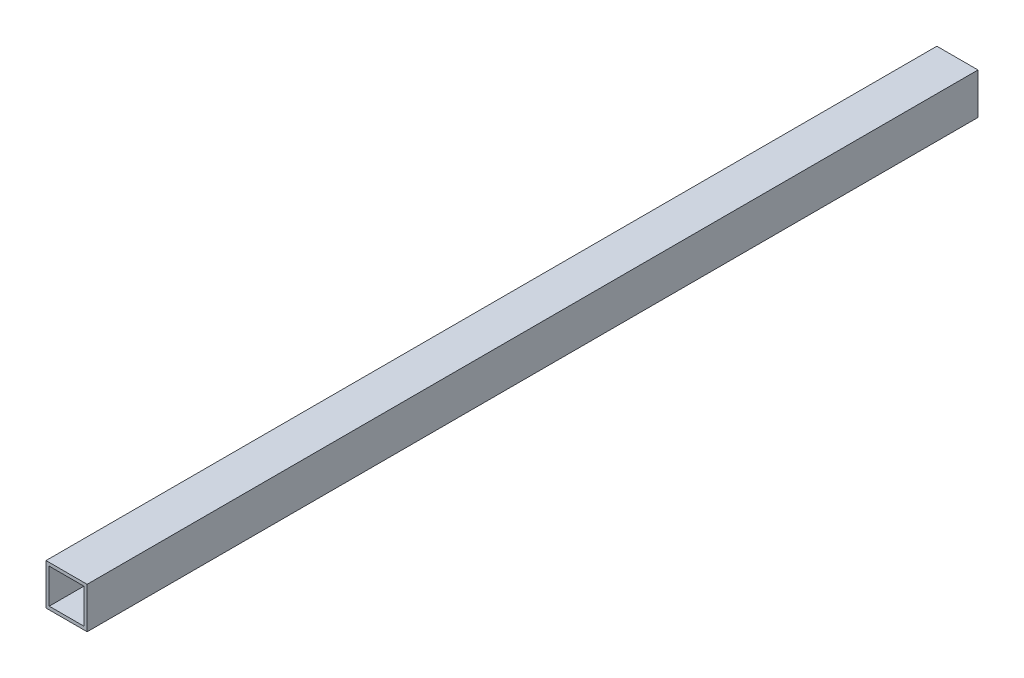
SolidWorks part; units mm, degrees
ref_plane "Front Plane" through (0, 0, 0) normal (0, 0, 1) x (1, 0, 0)
ref_plane "Top Plane" through (0, 0, 0) normal (0, 1, 0) x (1, 0, 0)
ref_plane "Right Plane" through (0, 0, 0) normal (1, 0, 0) x (0, 0, -1)
sketch "Sketch1" plane through (0, 0, 0) normal (0, 0, 1) x (1, 0, 0)
  line L0 (-10.7, 10.7) -> (10.7, 10.7)
  line L1 (-12.7, -12.7) -> (12.7, -12.7)
  line L2 (-12.7, -12.7) -> (-12.7, 12.7)
  line L3 (-12.7, 12.7) -> (12.7, 12.7)
  line L4 (12.7, -12.7) -> (12.7, 12.7)
  line L5 (-12.7, -12.7) -> (12.7, 12.7) construction
  line L6 (-12.7, 12.7) -> (12.7, -12.7) construction
  line L7 (10.7, -10.7) -> (10.7, 10.7)
  line L8 (-10.7, -10.7) -> (10.7, -10.7)
  line L9 (-10.7, -10.7) -> (-10.7, 10.7)
  point P0 (0, 0)
  dimension "D1" = 25.4
  dimension "D2" = 2
extrude "Boss-Extrude1" add sketch "Sketch1" along normal blind 550
